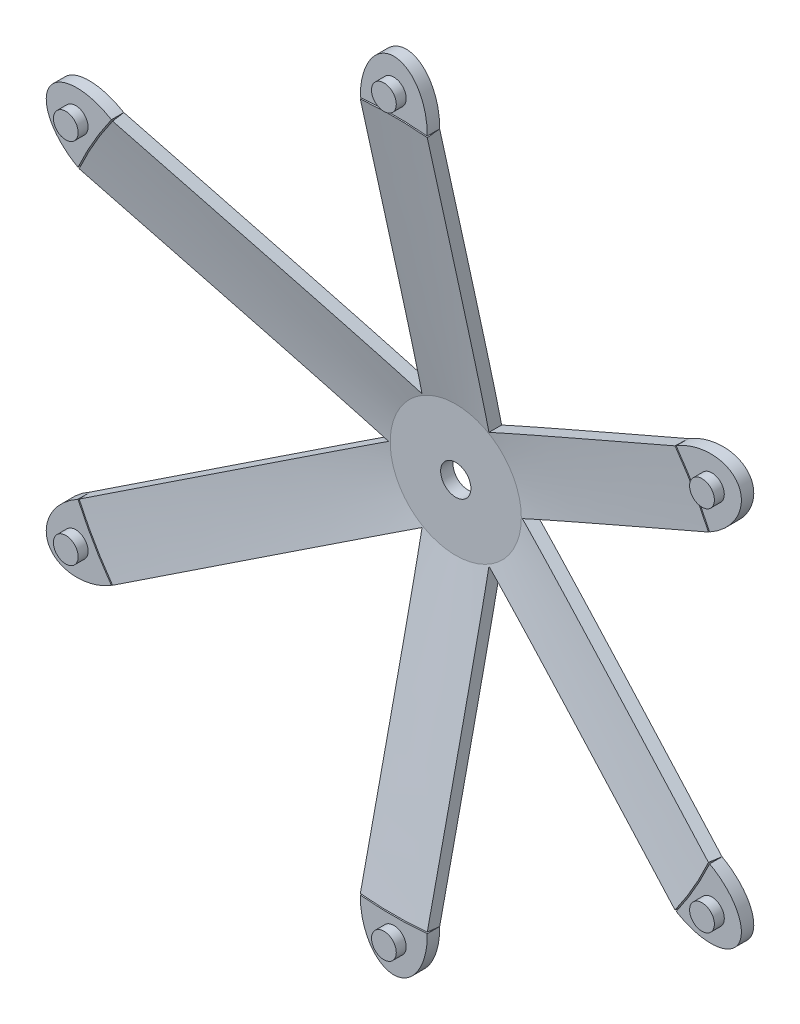
SolidWorks part; units mm, degrees
ref_plane "Front Plane" through (0, 0, 0) normal (0, 0, 1) x (1, 0, 0)
ref_plane "Top Plane" through (0, 0, 0) normal (0, 1, 0) x (1, 0, 0)
ref_plane "Right Plane" through (0, 0, 0) normal (1, 0, 0) x (0, 0, -1)
sketch "Sketch1" plane through (0, 0, 0) normal (0, 1, 0) x (1, 0, 0)
  line L0 (0, 47.8341) -> (0, -51.4495) construction
  line L1 (0, 0) -> (80, 0) construction
  line L4 (0, 15) -> (13.5, 15)
  line L5 (13.5, 15) -> (70, 2.5)
  line L6 (0, 12.5) -> (13.2268, 12.5)
  line L7 (13.2268, 12.5) -> (69.7268, 0)
  line L8 (13.2268, 12.5) -> (69.46, 0.059) construction
  line L10 (0, 12.5) -> (0, 15)
  line L11 (70, 2.5) -> (69.7268, 0)
  line L12 (0, 13.75) -> (70, 13.75) construction
  dimension "D1" = 2.5
  dimension "D2" = 70
  dimension "D4" = 13.5
  dimension "D5" = 15
  dimension "D6" = 2.5
revolve "Revolve1" add sketch "Sketch1" angle 360 about L10
hole_wizard "Ø6.1 (6.1) Diameter Hole1" positions "Sketch4" profile "Sketch5" hole size "Ø6.1" standard "ANSI Metric" end condition through all
sketch "Sketch4" plane through (0, 0, -15) normal (0, 0, -1) x (-1, 0, 0)
  point P0 (0, 0)
sketch "Sketch5" plane through (0, 0, -15) normal (1, 0, 0) x (0, 1, 0)
  line L0 (0, 0) -> (0, 15)
  line L1 (0, 15) -> (3.05, 15)
  line L2 (3.05, 15) -> (3.05, 0)
  line L5 (3.05, 0) -> (0, 0)
  line L11 (0, -6.35) -> (0, 107.95) construction
  dimension "Thru Hole Dia." = 6.1
  dimension "Thru Hole Depth" = 15
sketch "Sketch6" plane through (0, 0, 0) normal (0, 0, 1) x (1, 0, 0)
  line L0 (0, 13.5) -> (0, 70) construction
  line L1 (0, 0) -> (13.5, 0) construction
  line L2 (6.75, 11.6913) -> (6.75, 69.6738)
  line L14 (13.5, 0) -> (14.3089, 0) construction
  line L15 (13.5, 0) -> (63.7143, 28.9912)
  line L16 (-6.75, 11.6913) -> (-6.75, 69.6738)
  line L17 (6.75, 11.6913) -> (56.9643, 40.6826)
  line L18 (6.75, -11.6913) -> (56.9643, -40.6826)
  line L19 (13.5, 0) -> (63.7143, -28.9912)
  line L20 (-6.75, -11.6913) -> (-6.75, -69.6738)
  line L21 (6.75, -11.6913) -> (6.75, -69.6738)
  line L22 (-13.5, 0) -> (-63.7143, -28.9912)
  line L23 (-6.75, -11.6913) -> (-56.9643, -40.6826)
  line L24 (-6.75, 11.6913) -> (-56.9643, 40.6826)
  line L25 (-13.5, 0) -> (-63.7143, 28.9912)
  circle A1 centre (0, 0) radius 70 construction
  arc A2 (56.9643, 40.6826) -> (6.75, 69.6738) centre (0, 0) ccw
  arc A6 (63.7143, -28.9912) -> (69.6738, -6.75) centre (0, 0) ccw
  arc A7 (6.75, -69.6738) -> (56.9643, -40.6826) centre (0, 0) ccw
  arc A8 (-56.9643, -40.6826) -> (-6.75, -69.6738) centre (0, 0) ccw
  arc A9 (-6.75, 69.6738) -> (-56.9643, 40.6826) centre (0, 0) ccw
  arc A10 (-69.6738, -6.75) -> (-63.7143, -28.9912) centre (0, 0) ccw
  arc A11 (69.6738, -6.75) -> (63.7143, 28.9912) centre (0, 0) ccw
  circle A15 centre (0, 0) radius 13.5 construction
  arc A16 (-63.7143, 28.9912) -> (-69.6738, -6.75) centre (0, 0) ccw
  point P38 (0, 0)
  point P41 (0, 0)
  point P44 (0, 0)
  dimension "D2" = 6
  dimension "D1" = 6.75
extrude "Cut-Extrude6" cut sketch "Sketch6" against normal through all
sketch "Sketch7" plane through (0, 0, 0) normal (0, 0, 1) x (1, 0, 0)
  line L0 (0, 0) -> (0, 70) construction
  arc A0 (6.7466, 69.6741) -> (-6.7466, 69.6741) centre (0, 0) ccw
  arc A1 (63.7129, 28.9943) -> (56.9663, 40.6798) centre (0, 0) ccw
  arc A2 (56.9663, -40.6798) -> (63.7129, -28.9943) centre (0, 0) ccw
  arc A3 (-6.7466, -69.6741) -> (6.7466, -69.6741) centre (0, 0) ccw
  arc A4 (-63.7129, -28.9943) -> (-56.9663, -40.6798) centre (0, 0) ccw
  arc A5 (-56.9663, 40.6798) -> (-63.7129, 28.9943) centre (0, 0) ccw
  ellipse E0 centre (0, 70) end of major axis (0, 59.75) minor radius 6.75 (6.7466, 69.6741) -> (-6.7466, 69.6741) ccw
  ellipse E1 centre (60.6218, 35) end of major axis (51.745, 29.875) minor radius 6.75 (63.7129, 28.9943) -> (56.9663, 40.6798) ccw
  ellipse E2 centre (60.6218, -35) end of major axis (51.745, -29.875) minor radius 6.75 (56.9663, -40.6798) -> (63.7129, -28.9943) ccw
  ellipse E3 centre (0, -70) end of major axis (0, -59.75) minor radius 6.75 (-6.7466, -69.6741) -> (6.7466, -69.6741) ccw
  ellipse E4 centre (-60.6218, -35) end of major axis (-51.745, -29.875) minor radius 6.75 (-63.7129, -28.9943) -> (-56.9663, -40.6798) ccw
  ellipse E5 centre (-60.6218, 35) end of major axis (-51.745, 29.875) minor radius 6.75 (-56.9663, 40.6798) -> (-63.7129, 28.9943) ccw
  point P50 (0, 0)
  dimension "D1" = 140
  dimension "D2" = 20.5
  dimension "D3" = 13.5
extrude "Boss-Extrude1" add sketch "Sketch7" against normal blind 2.5 separate body
sketch "Sketch8" plane through (0, 0, 0) normal (0, 0, 1) x (1, 0, 0)
  line L0 (0, 0) -> (0, 74.0989) construction
  circle A0 centre (0, 0) radius 74.0989 construction
  circle A1 centre (0, 74.0989) radius 2.5
  circle A4 centre (0, 0) radius 70 construction
  circle A5 centre (64.1715, 37.0494) radius 2.5
  circle A6 centre (64.1715, -37.0494) radius 2.5
  circle A7 centre (0, -74.0989) radius 2.5
  circle A8 centre (-64.1715, -37.0494) radius 2.5
  circle A9 centre (-64.1715, 37.0494) radius 2.5
  point P18 (0, 0)
  dimension "D1" = 148.1978
  dimension "D2" = 5
  dimension "D3" = 140
  dimension "D4" = 6
extrude "Boss-Extrude2" add sketch "Sketch8" along normal blind 2
